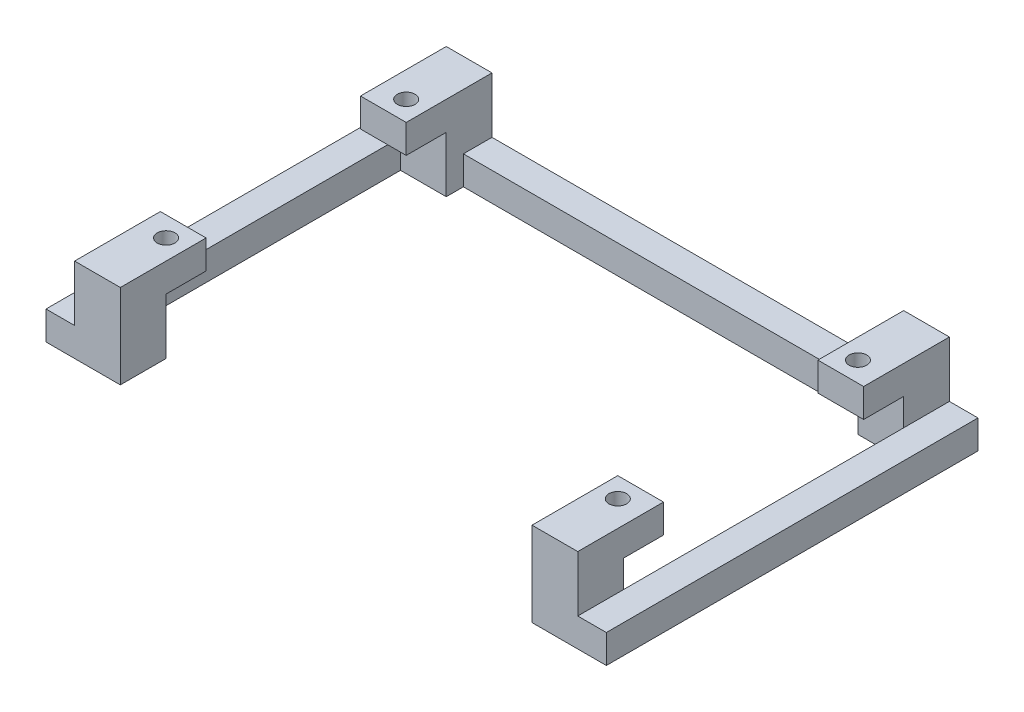
SolidWorks part; units mm, degrees
ref_plane "Front Plane" through (0, 0, 0) normal (0, 0, 1) x (1, 0, 0)
ref_plane "Top Plane" through (0, 0, 0) normal (0, 1, 0) x (1, 0, 0)
ref_plane "Right Plane" through (0, 0, 0) normal (1, 0, 0) x (0, 0, -1)
sketch "Sketch1" plane through (0, 0, 0) normal (0, 1, 0) x (1, 0, 0)
  line L0 (-36, -17.5) -> (36, 17.5) construction
  line L1 (-43, 24.5) -> (-36, 24.5)
  line L2 (-43, 24.5) -> (-43, 17.5)
  line L3 (-43, 17.5) -> (-36, 17.5)
  line L4 (-36, 24.5) -> (-36, 17.5)
  line L5 (36, 24.5) -> (43, 24.5)
  line L6 (36, 24.5) -> (36, 17.5)
  line L7 (36, 17.5) -> (43, 17.5)
  line L8 (43, 24.5) -> (43, 17.5)
  line L9 (-43, -17.5) -> (-36, -17.5)
  line L10 (-43, -17.5) -> (-43, -24.5)
  line L11 (-43, -24.5) -> (-36, -24.5)
  line L12 (-36, -17.5) -> (-36, -24.5)
  line L13 (36, -17.5) -> (43, -17.5)
  line L14 (36, -17.5) -> (36, -24.5)
  line L15 (36, -24.5) -> (43, -24.5)
  line L16 (43, -17.5) -> (43, -24.5)
  point P16 (0, 0)
  dimension "D1" = 7
  dimension "D2" = 79
  dimension "D3" = 42
extrude "Boss-Extrude1" add sketch "Sketch1" along normal blind 5
sketch "Sketch2" plane through (0, 5, 0) normal (0, 1, 0) x (1, 0, 0)
  line L0 (-36, 24.5) -> (-43, 24.5) construction
  line L1 (-36, 17.5) -> (-36, 24.5) construction
  line L2 (-36, -17.5) -> (-43, -17.5) construction
  line L3 (-43, -17.5) -> (-43, -24.5) construction
  line L4 (43, -17.5) -> (36, -17.5) construction
  line L5 (36, -17.5) -> (36, -24.5) construction
  line L6 (43, 24.5) -> (36, 24.5) construction
  line L7 (36, 24.5) -> (36, 17.5) construction
  circle A0 centre (-39.5, 21) radius 1.55
  circle A1 centre (39.5, 21) radius 1.55
  circle A2 centre (39.5, -21) radius 1.55
  circle A3 centre (-39.5, -21) radius 1.55
  point P10 (-39.5, 24.5)
  point P13 (-36, 21)
  point P17 (-39.5, -17.5)
  point P20 (-43, -21)
  point P23 (39.5, -17.5)
  point P26 (36, -21)
  point P29 (39.5, 24.5)
  point P32 (36, 21)
  dimension "D1" = 3.1
extrude "Cut-Extrude1" cut sketch "Sketch2" against normal through all
sketch "Sketch4" plane through (0, 5, 0) normal (0, 1, 0) x (1, 0, 0)
  line L1 (36, 32.5) -> (44, 32.5)
  line L2 (36, 32.5) -> (36, 24.5)
  line L3 (36, 24.5) -> (44, 24.5)
  line L4 (44, 32.5) -> (44, 24.5)
  line L5 (36, -32.5) -> (44, -32.5)
  line L6 (36, -32.5) -> (36, -24.5)
  line L7 (36, -24.5) -> (44, -24.5)
  line L8 (44, -32.5) -> (44, -24.5)
  line L9 (-36, -32.5) -> (-44, -32.5)
  line L10 (-36, -32.5) -> (-36, -24.5)
  line L11 (-36, -24.5) -> (-44, -24.5)
  line L12 (-44, -32.5) -> (-44, -24.5)
  line L13 (-36, 32.5) -> (-44, 32.5)
  line L14 (-36, 32.5) -> (-36, 24.5)
  line L15 (-36, 24.5) -> (-44, 24.5)
  line L16 (-44, 32.5) -> (-44, 24.5)
  dimension "D1" = 8
extrude "Boss-Extrude3" add sketch "Sketch4" against normal blind 14.76
sketch "Sketch5" plane through (0, -9.76, 0) normal (0, -1, 0) x (1, 0, 0)
  line L0 (-49, 32.5) -> (-49, -32.5)
  line L1 (44, -32.5) -> (36, -32.5) construction
  line L3 (-49, -32.5) -> (49, -32.5)
  line L4 (49, -32.5) -> (49, 32.5)
  line L6 (49, 32.5) -> (44, 32.5)
  line L7 (44, 32.5) -> (44, -27.5)
  line L8 (44, -27.5) -> (-44, -27.5)
  line L9 (-44, -27.5) -> (-44, 32.5)
  line L10 (-44, 32.5) -> (-49, 32.5)
  dimension "D1" = 5
  dimension "D2" = 5
extrude "Boss-Extrude4" add sketch "Sketch5" against normal blind 5
sketch "Sketch6" plane through (0, -4.76, 0) normal (0, 1, 0) x (-1, 0, 0)
  line L0 (-49, -32.5) -> (-44, -32.5) construction
  line L1 (-49, 32.5) -> (-49, -32.5) construction
  line L2 (-44, 32.5) -> (-49, 32.5) construction
  line L3 (49, -32.5) -> (49, 32.5) construction
  circle A0 centre (40, 28.5) radius 1.0795
  circle A1 centre (40, -28.5) radius 1.0795
  circle A2 centre (-40, -28.5) radius 1.0795
  circle A3 centre (-40, 28.5) radius 1.0795
  dimension "D1" = 2.159
  dimension "D2" = 4
  dimension "D3" = 9
  dimension "D4" = 4
  dimension "D5" = 9
extrude "Cut-Extrude2" cut sketch "Sketch6" against normal blind 10
sketch "Sketch7" plane through (0, 5, 0) normal (0, 1, 0) x (1, 0, 0)
  line L1 (44, -24.5) -> (43, -24.5)
  line L2 (44, -24.5) -> (44, -17.5)
  line L3 (44, -17.5) -> (43, -17.5)
  line L4 (43, -24.5) -> (43, -17.5)
  line L5 (44, 24.5) -> (43, 24.5)
  line L6 (44, 24.5) -> (44, 17.5)
  line L7 (44, 17.5) -> (43, 17.5)
  line L8 (43, 24.5) -> (43, 17.5)
  line L9 (-44, 24.5) -> (-43, 24.5)
  line L10 (-44, 24.5) -> (-44, 17.5)
  line L11 (-44, 17.5) -> (-43, 17.5)
  line L12 (-43, 24.5) -> (-43, 17.5)
  line L13 (-44, -24.5) -> (-43, -24.5)
  line L14 (-44, -24.5) -> (-44, -17.5)
  line L15 (-44, -17.5) -> (-43, -17.5)
  line L16 (-43, -24.5) -> (-43, -17.5)
extrude "Boss-Extrude5" add sketch "Sketch7" against normal blind 5
